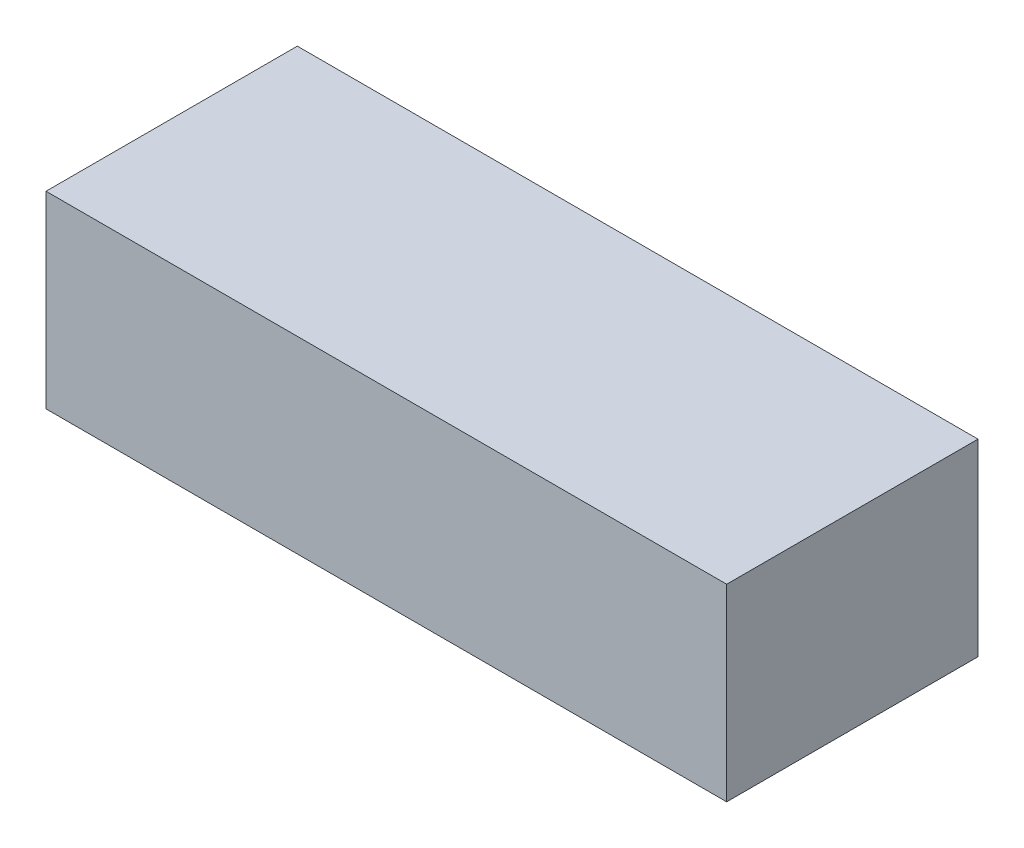
SolidWorks part; units mm, degrees
ref_plane "Front Plane" through (0, 0, 0) normal (0, 0, 1) x (1, 0, 0)
ref_plane "Top Plane" through (0, 0, 0) normal (0, 1, 0) x (1, 0, 0)
ref_plane "Right Plane" through (0, 0, 0) normal (1, 0, 0) x (0, 0, -1)
sketch "Sketch2" plane through (0, 0, 0) normal (1, 0, 0) x (0, 0, -1)
  line L1 (-12, -9) -> (12, -9)
  line L2 (-12, -9) -> (-12, 9)
  line L3 (-12, 9) -> (12, 9)
  line L4 (12, -9) -> (12, 9)
  line L5 (0, 9) -> (0, -9) construction
  line L6 (-12, 0) -> (12, 0) construction
  point P0 (0, 0)
  dimension "D1" = 24
  dimension "D2" = 18
extrude "Boss-Extrude1" add sketch "Sketch2" along normal blind 65
